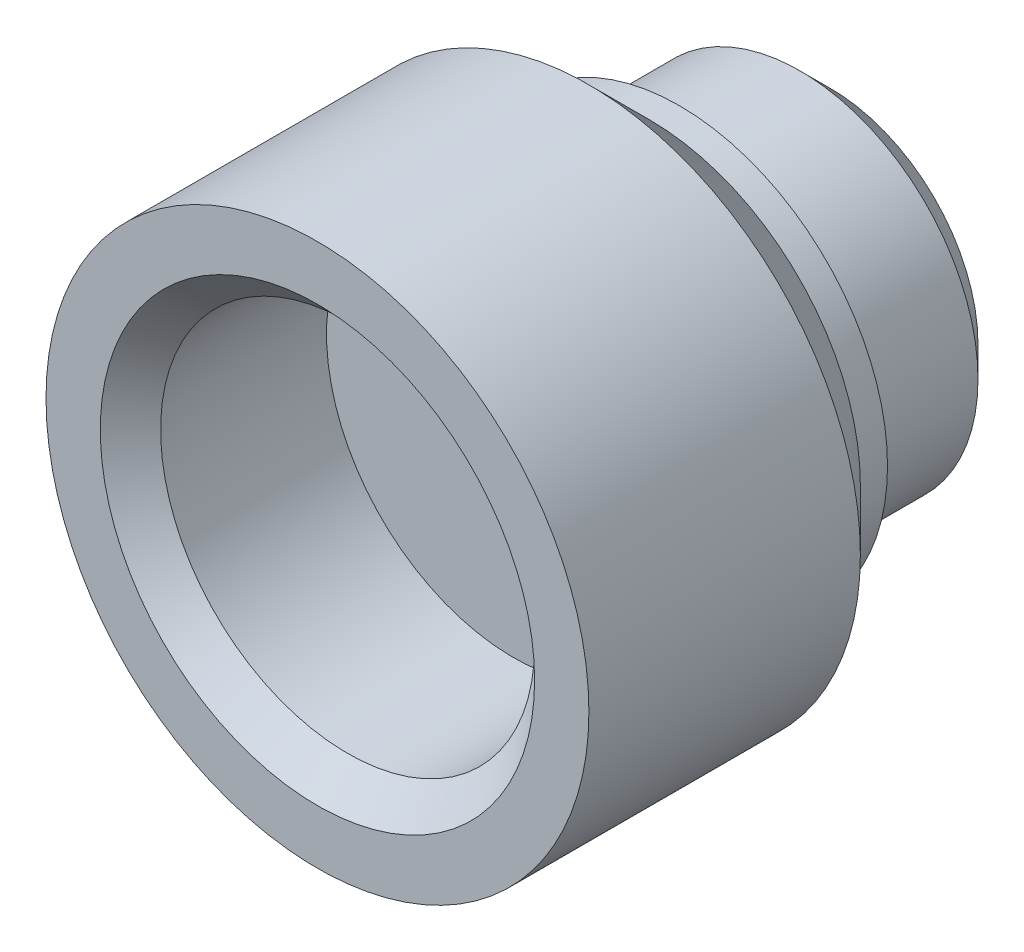
SolidWorks part; units mm, degrees
ref_plane "Front Plane" through (0, 0, 0) normal (0, 0, 1) x (1, 0, 0)
ref_plane "Top Plane" through (0, 0, 0) normal (0, 1, 0) x (1, 0, 0)
ref_plane "Right Plane" through (0, 0, 0) normal (1, 0, 0) x (0, 0, -1)
sketch "Sketch1" plane through (0, 0, 0) normal (0, 0, 1) x (1, 0, 0)
  circle A0 centre (0, 0) radius 2.95
  circle A1 centre (0, 0) radius 1
  dimension "D1" = 5.9
  dimension "D2" = 2
extrude "Boss-Extrude1" add sketch "Sketch1" along normal blind 3
sketch "Sketch2" plane through (0, 0, 3) normal (0, 0, 1) x (1, 0, 0)
  circle A0 centre (0, 0) radius 1
  circle A1 centre (0, 0) radius 4.5
  circle A2 centre (0, 0) radius 1 construction
  dimension "D1" = 9
extrude "Boss-Extrude2" add sketch "Sketch2" along normal blind 5.5
sketch "Sketch3" plane through (0, 0, 8.5) normal (0, 0, 1) x (1, 0, 0)
  circle A0 centre (0, 0) radius 3.1
  dimension "D1" = 6.2
extrude "Cut-Extrude1" cut sketch "Sketch3" against normal blind 3.25
chamfer "Chamfer1" distance 0.5 angle 45 1 edges at (3.1, 0, 8.5)
chamfer "Chamfer2" distance 0.5 angle 45 1 edges at (2.95, 0, 0)
sketch "Sketch4" plane through (0, 0, 3) normal (0, 0, -1) x (-1, 0, 0)
  circle A0 centre (0, 0) radius 1
  circle A1 centre (0, 0) radius 3.45
  circle A2 centre (0, 0) radius 1 construction
  circle A3 centre (0, 0) radius 2.95 construction
  dimension "D1" = 0.5
extrude "Boss-Extrude3" add sketch "Sketch4" along normal blind 0.5
chamfer "Chamfer3" distance 1 angle 45 1 edges at (4.5, 0, 3)
